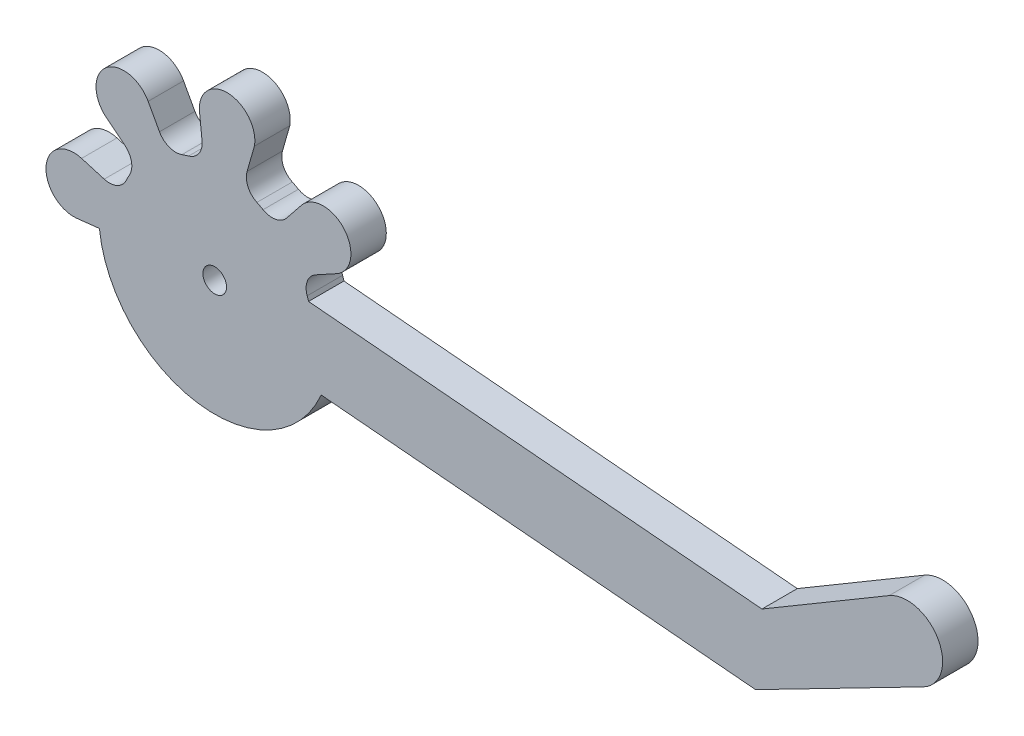
SolidWorks part; units mm, degrees
ref_plane "Alzado" through (0, 0, 0) normal (0, 0, 1) x (1, 0, 0)
ref_plane "Planta" through (0, 0, 0) normal (0, 1, 0) x (1, 0, 0)
ref_plane "Vista lateral" through (0, 0, 0) normal (1, 0, 0) x (0, 0, -1)
sketch "Model" plane through (0, 0, 0) normal (0, 0, 1) x (1, 0, 0)
  line L0 (17.8616, 18.2071) -> (56.2774, 14.8461)
  line L1 (55.7362, 8.6597) -> (18.9349, 11.8794)
  line L2 (13.2728, 27.3091) -> (12.6532, 25.1469)
  line L3 (8.8373, 25.4808) -> (8.6026, 27.7177)
  line L4 (2.2965, 21.8815) -> (0.7345, 23.1318)
  line L5 (-1.3697, 19.0897) -> (0.5504, 18.5273)
  line L6 (0.139, 14.7028) -> (-1.7721, 14.491)
  line L7 (20.225, 21.4266) -> (18.4696, 20.4665)
  line L8 (16.0074, 23.4009) -> (17.2577, 24.9629)
  line L9 (13.4846, 23.289) -> (14.0086, 23.0162)
  line L10 (4.2707, 26.0991) -> (5.2309, 24.3437)
  line L11 (56.2774, 14.8461) -> (67.0579, 21.2233)
  line L12 (55.7362, 8.6597) -> (69.9644, 15.977)
  circle A0 centre (9.9116, 15.7857) radius 1
  arc A1 (4.2707, 26.0991) -> (4.157, 26.2858) centre (2.2055, 24.9695) ccw
  arc A2 (13.2728, 27.3091) -> (8.6026, 27.7177) centre (10.9565, 27.7287) ccw
  arc A3 (4.157, 26.2858) -> (4.14, 26.3107) centre (2.2055, 24.9695) ccw
  arc A4 (4.14, 26.3107) -> (0.5488, 23.2973) centre (2.2055, 24.9695) ccw
  arc A5 (0.5488, 23.2973) -> (0.5703, 23.2762) centre (2.2055, 24.9695) ccw
  arc A6 (0.5703, 23.2762) -> (0.7345, 23.1318) centre (2.2055, 24.9695) ccw
  arc A7 (2.6812, 19.8827) -> (2.2965, 21.8815) centre (1.3158, 20.6563) ccw
  arc A8 (2.6812, 19.8827) -> (2.4084, 19.3587) centre (9.9116, 15.7857) ccw
  arc A9 (0.5504, 18.5273) -> (2.4084, 19.3587) centre (0.9915, 20.0334) ccw
  arc A10 (-1.3697, 19.0897) -> (-1.5822, 19.1413) centre (-2.0313, 16.8306) ccw
  arc A11 (-1.5822, 19.1413) -> (-1.6118, 19.1469) centre (-2.0313, 16.8306) ccw
  arc A12 (-1.6118, 19.1469) -> (-2.0203, 14.4767) centre (-2.0313, 16.8306) ccw
  arc A13 (-2.0203, 14.4767) -> (-1.9902, 14.477) centre (-2.0313, 16.8306) ccw
  arc A14 (-1.9902, 14.477) -> (-1.7721, 14.491) centre (-2.0313, 16.8306) ccw
  arc A15 (0.139, 14.7028) -> (18.9349, 11.8794) centre (9.9116, 15.7857) ccw
  arc A16 (17.8616, 18.2071) -> (17.7437, 18.5649) centre (9.9116, 15.7857) ccw
  arc A17 (18.4696, 20.4665) -> (17.7437, 18.5649) centre (19.2227, 19.0897) ccw
  arc A18 (20.225, 21.4266) -> (20.4117, 21.5403) centre (19.0954, 23.4919) ccw
  arc A19 (20.4117, 21.5403) -> (20.4366, 21.5573) centre (19.0954, 23.4919) ccw
  arc A20 (20.4366, 21.5573) -> (17.4232, 25.1486) centre (19.0954, 23.4919) ccw
  arc A21 (17.4232, 25.1486) -> (17.4021, 25.127) centre (19.0954, 23.4919) ccw
  arc A22 (17.4021, 25.127) -> (17.2577, 24.9629) centre (19.0954, 23.4919) ccw
  arc A23 (7.6959, 23.7955) -> (8.8373, 25.4808) centre (7.2775, 25.308) ccw
  arc A24 (14.0086, 23.0162) -> (16.0074, 23.4009) centre (14.7822, 24.3816) ccw
  arc A25 (7.6959, 23.7955) -> (7.1325, 23.6178) centre (9.9116, 15.7857) ccw
  arc A26 (5.2309, 24.3437) -> (7.1325, 23.6178) centre (6.6077, 25.0968) ccw
  arc A27 (12.6532, 25.1469) -> (13.4846, 23.289) centre (14.1593, 24.7059) ccw
  arc A28 (69.9644, 15.977) -> (67.0579, 21.2233) centre (68.5853, 18.6412) ccw
extrude "Saliente-Extruir1" add sketch "Model" along normal blind 3
